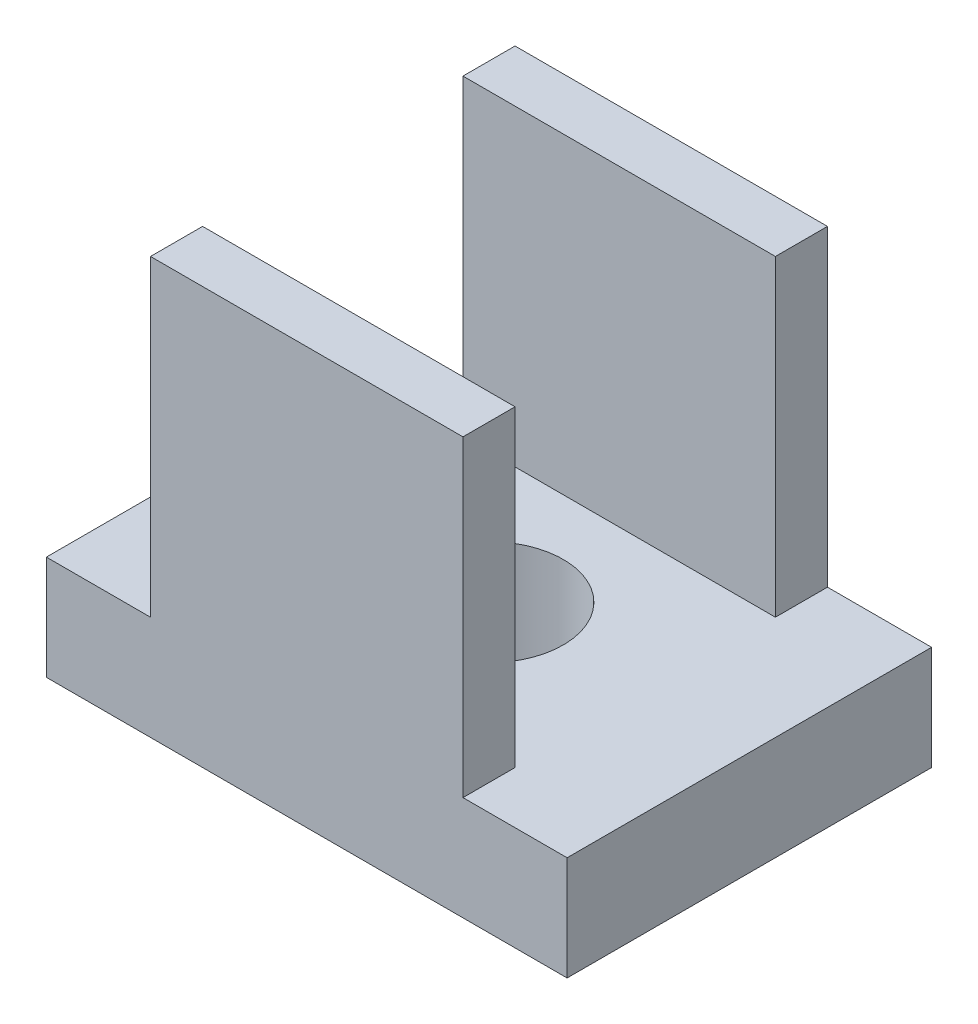
SolidWorks part; units mm, degrees
ref_plane "Front Plane" through (0, 0, 0) normal (0, 0, 1) x (1, 0, 0)
ref_plane "Top Plane" through (0, 0, 0) normal (0, 1, 0) x (1, 0, 0)
ref_plane "Right Plane" through (0, 0, 0) normal (1, 0, 0) x (0, 0, -1)
sketch "Sketch1" plane through (0, 0, 0) normal (0, 1, 0) x (1, 0, 0)
  line L1 (-5, 3.5) -> (5, 3.5)
  line L2 (-5, 3.5) -> (-5, -3.5)
  line L3 (-5, -3.5) -> (5, -3.5)
  line L4 (5, 3.5) -> (5, -3.5)
  line L5 (-5, 3.5) -> (5, -3.5) construction
  line L6 (-5, -3.5) -> (5, 3.5) construction
  point P0 (0, 0)
  dimension "D1" = 10
  dimension "D2" = 7
extrude "Boss-Extrude1" add sketch "Sketch1" along normal blind 2
sketch "Sketch2" plane through (0, 2, 0) normal (0, 1, 0) x (1, 0, 0)
  line L0 (-5.5453, 0) -> (5.7149, 0) construction
  line L1 (0, 4.0185) -> (0, -4.0927) construction
  circle A0 centre (0, 0) radius 1.425
  dimension "D1" = 2.85
extrude "Cut-Extrude1" cut sketch "Sketch2" against normal through all
sketch "Sketch3" plane through (0, 2, 0) normal (0, 1, 0) x (1, 0, 0)
  line L0 (5, 3.5) -> (-5, 3.5) construction
  line L1 (-3, 3.5) -> (3, 3.5)
  line L2 (-3, 3.5) -> (-3, 2.5)
  line L3 (-3, 2.5) -> (3, 2.5)
  line L4 (3, 3.5) -> (3, 2.5)
  line L6 (-3, -2.5) -> (3, -2.5)
  line L7 (-3, -2.5) -> (-3, -3.5)
  line L8 (-3, -3.5) -> (3, -3.5)
  line L9 (3, -2.5) -> (3, -3.5)
  line L10 (-5, -3.5) -> (5, -3.5) construction
  line L11 (0, 3.9124) -> (0, -3.9124) construction
  point P4 (0, 0)
  dimension "D1" = 1
  dimension "D2" = 6
extrude "Boss-Extrude2" add sketch "Sketch3" along normal blind 6
